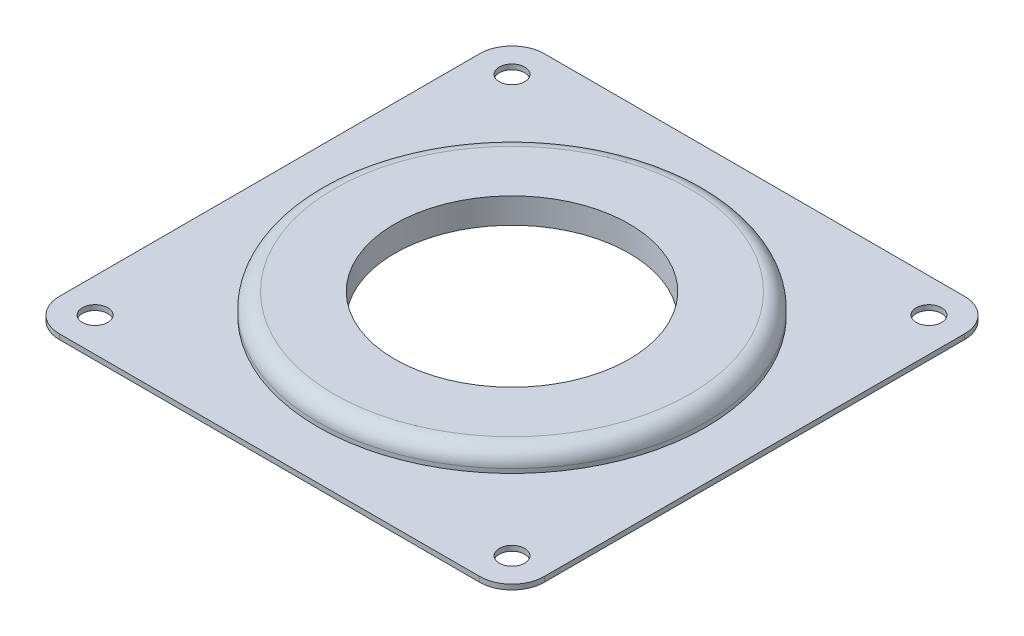
SolidWorks part; units mm, degrees
ref_plane "Front Plane" through (0, 0, 0) normal (0, 0, 1) x (1, 0, 0)
ref_plane "Top Plane" through (0, 0, 0) normal (0, 1, 0) x (1, 0, 0)
ref_plane "Right Plane" through (0, 0, 0) normal (1, 0, 0) x (0, 0, -1)
sketch "Sketch1" plane through (0, 0, 0) normal (0, 1, 0) x (1, 0, 0)
  line L1 (-38.1, -38.1) -> (38.1, -38.1)
  line L2 (-38.1, -38.1) -> (-38.1, 38.1)
  line L3 (-38.1, 38.1) -> (38.1, 38.1)
  line L4 (38.1, -38.1) -> (38.1, 38.1)
  line L5 (-38.1, -38.1) -> (38.1, 38.1) construction
  line L6 (-38.1, 38.1) -> (38.1, -38.1) construction
  circle A0 centre (-32.75, 32.75) radius 2
  circle A1 centre (32.75, 32.75) radius 2
  circle A2 centre (32.75, -32.75) radius 2
  circle A3 centre (-32.75, -32.75) radius 2
  circle A4 centre (0, 0) radius 18.415
  point P0 (0, 0)
  point P17 (0, 0)
  dimension "D3" = 4
  dimension "D5" = 36.83
  dimension "D1" = 76.2
  dimension "D4" = 65.5
  dimension "D2" = 4
extrude "Boss-Extrude1" add sketch "Sketch1" along normal blind 0.8
fillet "Fillet1" radius 5.08 4 edges at (38.1, 0.4, -38.1) (38.1, 0.4, 38.1) (-38.1, 0.4, -38.1) (-38.1, 0.4, 38.1)
sketch "Sketch2" plane through (0, 0.8, 0) normal (0, 1, 0) x (1, 0, 0)
  circle A0 centre (0, 0) radius 18.415 construction
  circle A1 centre (0, 0) radius 18.415
  circle A2 centre (0, 0) radius 30.48
  dimension "D1" = 60.96
extrude "Boss-Extrude2" add sketch "Sketch2" along normal blind 3.2
fillet "Fillet2" radius 2.54 1 edges at (0, 4, 30.48)
